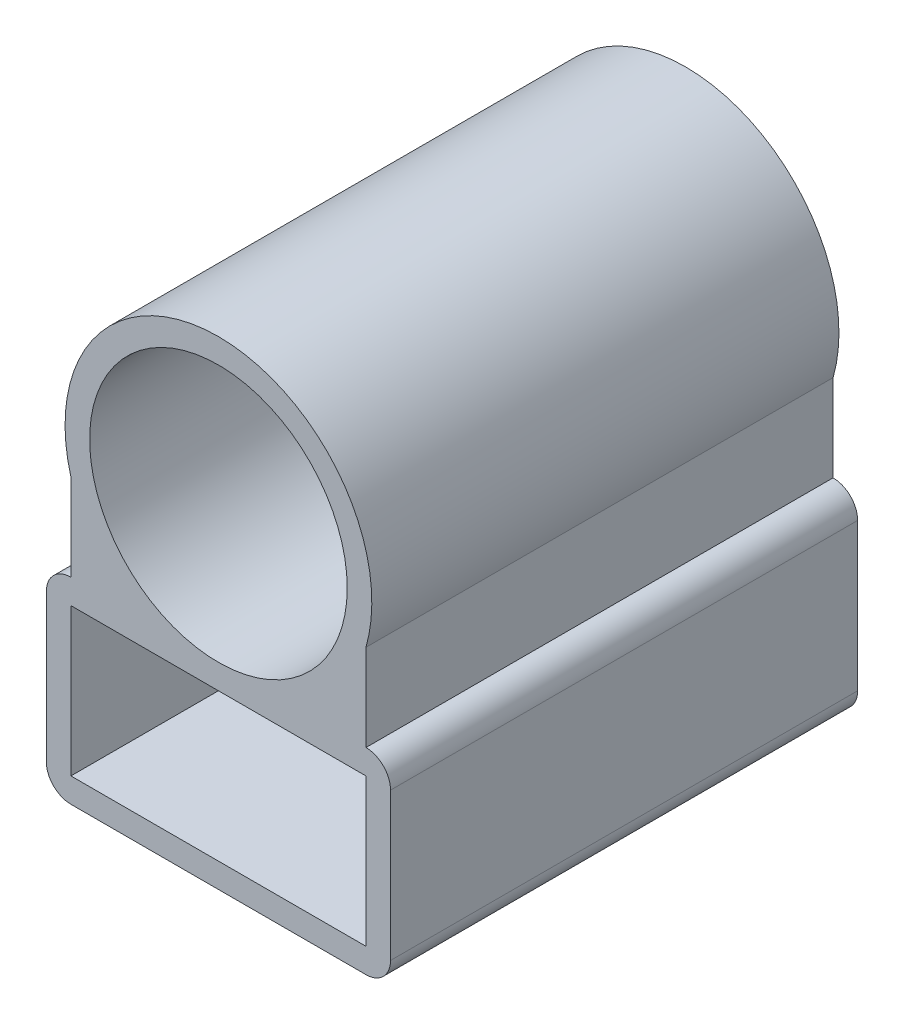
SolidWorks part; units mm, degrees
ref_plane "Front Plane" through (0, 0, 0) normal (0, 0, 1) x (1, 0, 0)
ref_plane "Top Plane" through (0, 0, 0) normal (0, 1, 0) x (1, 0, 0)
ref_plane "Right Plane" through (0, 0, 0) normal (1, 0, 0) x (0, 0, -1)
sketch "Sketch1" plane through (0, 0, 0) normal (0, 0, 1) x (1, 0, 0)
  line L0 (-1002.3484, -62.3875) -> (48997.6516, -62.3875) construction
  line L1 (-1002.571, -122.3875) -> (48997.429, -122.3875) construction
  line L2 (-60, -62.3875) -> (-60, -122.3875)
  line L3 (-60, -122.3875) -> (60, -122.3875)
  line L4 (60, -122.3875) -> (60, -62.3875)
  line L5 (60, -62.3875) -> (-60, -62.3875)
  line L6 (0, -1000) -> (0, 49000) construction
  line L7 (-1000, -52.3875) -> (49000, -52.3875) construction
  line L8 (60, -52.3875) -> (-60, -52.3875) construction
  line L9 (-70, -62.3875) -> (-70, -122.3875)
  line L10 (-60, -132.3875) -> (60, -132.3875)
  line L11 (70, -122.3875) -> (70, -62.3875)
  line L12 (70, -52.3875) -> (-70, -52.3875) construction
  line L13 (70, -132.3875) -> (70, -52.3875) construction
  line L14 (-70, -132.3875) -> (70, -132.3875) construction
  line L15 (-70, -52.3875) -> (-70, -132.3875) construction
  line L16 (-60, -52.3875) -> (-60, -17.0939)
  line L17 (60, -52.3875) -> (60, -17.0939)
  circle A0 centre (0, 0) radius 52.3875
  arc A1 (60, -17.0939) -> (-60, -17.0939) centre (0, 0) ccw
  arc A2 (60, -52.3875) -> (70, -62.3875) centre (60, -62.3875) cw
  arc A3 (60, -132.3875) -> (70, -122.3875) centre (60, -122.3875) ccw
  arc A4 (-70, -122.3875) -> (-60, -132.3875) centre (-60, -122.3875) ccw
  arc A5 (-60, -52.3875) -> (-70, -62.3875) centre (-60, -62.3875) ccw
  circle A6 centre (0, 0) radius 62.3875 construction
  point P11 (0, -62.3875)
  dimension "D1" = 104.775
  dimension "D7" = 10
  dimension "D3" = 120
  dimension "D4" = 60
  dimension "D5" = 10
  dimension "D6" = 10
  dimension "D2" = 10
extrude "Boss-Extrude1" add sketch "Sketch1" along normal blind 190
